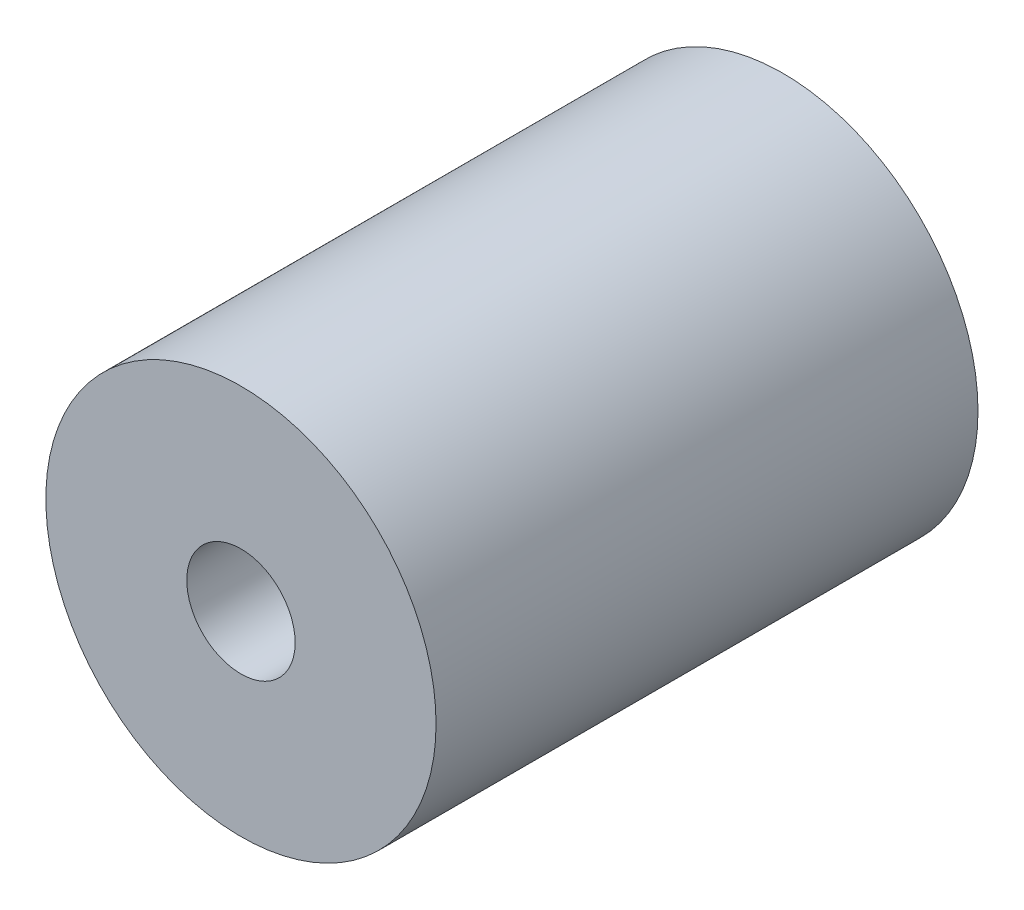
SolidWorks part; units mm, degrees
ref_plane "Front Plane" through (0, 0, 0) normal (0, 0, 1) x (1, 0, 0)
ref_plane "Top Plane" through (0, 0, 0) normal (0, 1, 0) x (1, 0, 0)
ref_plane "Right Plane" through (0, 0, 0) normal (1, 0, 0) x (0, 0, -1)
sketch "Sketch1" plane through (0, 0, 0) normal (0, 0, 1) x (1, 0, 0)
  circle A0 centre (0, 0) radius 9
  dimension "D1" = 18
extrude "Boss-Extrude1" add sketch "Sketch1" along normal mid plane 25
sketch "Sketch2" plane through (0, 0, 12.5) normal (0, 0, 1) x (1, 0, 0)
  circle A0 centre (0, 0) radius 2.5
  dimension "D1" = 5
extrude "Cut-Extrude1" cut sketch "Sketch2" against normal through all
sketch "Sketch3" plane through (0, 0, -12.5) normal (0, 0, -1) x (-1, 0, 0)
  circle A0 centre (0, 0) radius 4
  dimension "D1" = 8
extrude "Cut-Extrude2" cut sketch "Sketch3" against normal blind 17.5
